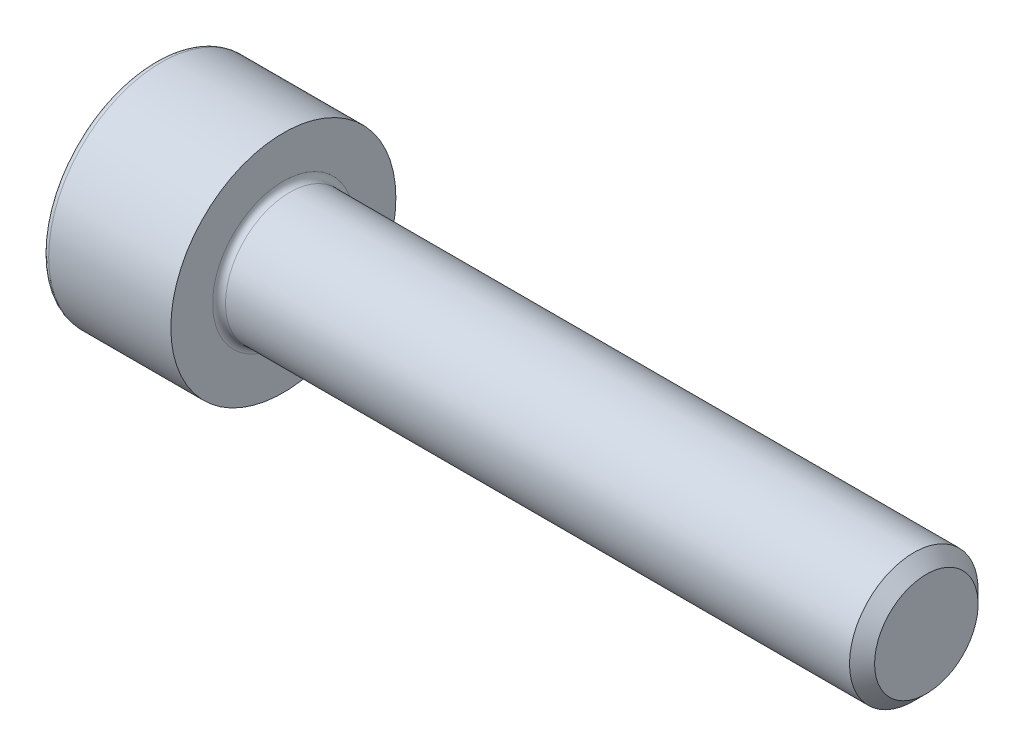
SolidWorks part; units mm, degrees
ref_plane "Plane1" through (0, 0, 0) normal (0, 0, 1) x (1, 0, 0)
ref_plane "Plane2" through (0, 0, 0) normal (0, 1, 0) x (1, 0, 0)
ref_plane "Plane3" through (0, 0, 0) normal (1, 0, 0) x (0, 0, -1)
sketch "BodySke" plane through (0, 0, 0) normal (0, 0, 1) x (1, 0, 0)
  line L0 (0, 0) -> (0, 3.5)
  line L1 (0, 3.5) -> (4, 3.5)
  line L2 (4, 3.5) -> (4, 2)
  line L3 (4, 2) -> (23.61, 2)
  line L4 (24, 1.61) -> (24, 0)
  line L5 (24, 0) -> (0, 0)
  line L6 (-31.75, 0) -> (127, 0) construction
  line L8 (24, 1.61) -> (23.61, 2)
  line L10 (24, -1.61) -> (23.61, -2) construction
  line L11 (3.3, 9.525) -> (3.3, 3.175) construction
  line L12 (4, 9.525) -> (4, 3.175) construction
  line L13 (-21, 9.525) -> (-21, 3.175) construction
  dimension "Diameter" = 4
  dimension "Head_ht" = 4
  dimension "Length" = 20
  dimension "Body_ch_ang" = 45
  dimension "Head_dia" = 7
  dimension "Minor_dia" = 3.22
  dimension "Advance" = 0.7
  dimension "Thread_nom" = 20
  dimension "Thread_length" = 45
revolve "Base-Revolve" add sketch "BodySke" angle 360 about L6
cosmetic thread "ThreadCosmetic" parameters "Thread_length"=17.9, "Thread_minor"=3.22
fillet "Fillet1" radius 0.2 1 edges at (4, 0, 2)
fillet "Fillet2" radius 0.2 1 edges at (0, 0, 3.5)
sketch "Sketch2" plane through (0, 0, 0) normal (0, 0, 1) x (1, 0, 0)
  line L0 (0, 1.5355) -> (2, 1.5355)
  line L1 (2, 1.5355) -> (2.8865, 0)
  line L2 (-31.75, 0) -> (127, 0) construction
  line L3 (2.8865, 0) -> (0, 0)
  line L4 (0, 0) -> (0, 1.5355)
  line L6 (0, 0) -> (47.625, 0) construction
  dimension "D1" = 1.5355
  dimension "D2" = 60
  dimension "Depth" = 2
revolve "Hex-PreBroach" cut sketch "Sketch2" angle 360 about L6
sketch "Sketch3" plane through (0, 0, 0) normal (-1, 0, 0) x (0, 0.5, 0.866)
  line L0 (0.8865, 1.5355) -> (-0.8865, 1.5355)
  line L1 (-0.8865, 1.5355) -> (-1.773, 0)
  line L2 (0.8865, 1.5355) -> (1.773, 0)
  line L3 (0.8865, -1.5355) -> (1.773, 0)
  line L4 (0.8865, -1.5355) -> (-0.8865, -1.5355)
  line L5 (-0.8865, -1.5355) -> (-1.773, 0)
  dimension "D1" = 1.5355
  dimension "D2" = 1.5355
  dimension "Hex_size" = 3.071
extrude "Hex" cut sketch "Sketch3" against normal blind 2
sketch "ThdSchSke" plane through (0, 0, 0) normal (0, 0, 1) x (1, 0, 0)
  line L0 (6.1, -1.61) -> (5.8269, -2)
  line L1 (6.1, -1.61) -> (6.3731, -2)
  line L2 (6.3731, -2) -> (6.3731, -2.5)
  line L3 (-3.175, 0) -> (5.1513, 0) construction
  line L4 (0, 3.3) -> (0, -3.3) construction
  line L5 (6.3731, -2.5) -> (5.8269, -2.5)
  line L6 (5.8269, -2.5) -> (5.8269, -2)
  dimension "Thread_minor" = 3.22
  dimension "Diameter" = 4
  dimension "Start" = 6.1
  dimension "SideAngle" = 55
  dimension "VeeAngle" = 70
  dimension "Overcut" = 5
revolve "ThreadSchematic" [suppressed] cut sketch "ThdSchSke" angle 360 about L3
pattern_linear "ThdSchPat" [suppressed]
equation "\"D2@Sketch3\" = \"Hex_size@Sketch3\" / 2"
equation "\"D1@Sketch3\" = \"Hex_size@Sketch3\" / 2"
equation "\"D1@Sketch2\" = \"Hex_size@Sketch3\" / 2"
equation "\"Thread_minor@ThreadCosmetic\"  =  \"Minor_dia@BodySke\""
equation "\"Depth@Sketch2\" =  \"Key_eng@Hex\""
equation "\"Thread_length@ThreadCosmetic\" = ((sgn( (\"Length@BodySke\" - \"Advance@BodySke\" * 3.0) - \"Thread_nom@BodySke\" )-1)*( (\"Length@BodySke\" - \"Advance@BodySke\" * 3.0) - \"Thread_nom@BodySke\" ))/-2+ \"Thread_nom@BodySke\""
equation "\"Thread_minor@ThdSchSke\" = \"Minor_dia@BodySke\""
equation "\"Diameter@ThdSchSke\" = \"Diameter@BodySke\""
equation "\"Overcut@ThdSchSke\" = \"Diameter@BodySke\" * 1.25"
equation "\"Start@ThdSchSke\" = \"Head_ht@BodySke\" + \"Length@BodySke\" - \"Thread_length@ThreadCosmetic\"  '---Non-countersunk---"
equation "\"Num_threads@ThdSchPat\" = int( \"Thread_length@ThreadCosmetic\" / \"Advance@BodySke\" + 0.999 )  + 1"
equation "\"Advance@ThdSchPat\" = \"Thread_length@ThreadCosmetic\" /  (\"Num_threads@ThdSchPat\" - 1) 'relax it"
equation "\"Num_threads@ThdSchPat\" = \"Num_threads@ThdSchPat\" - sgn( \"Num_threads@ThdSchPat\" - 1) '---chamfered tips only---"
